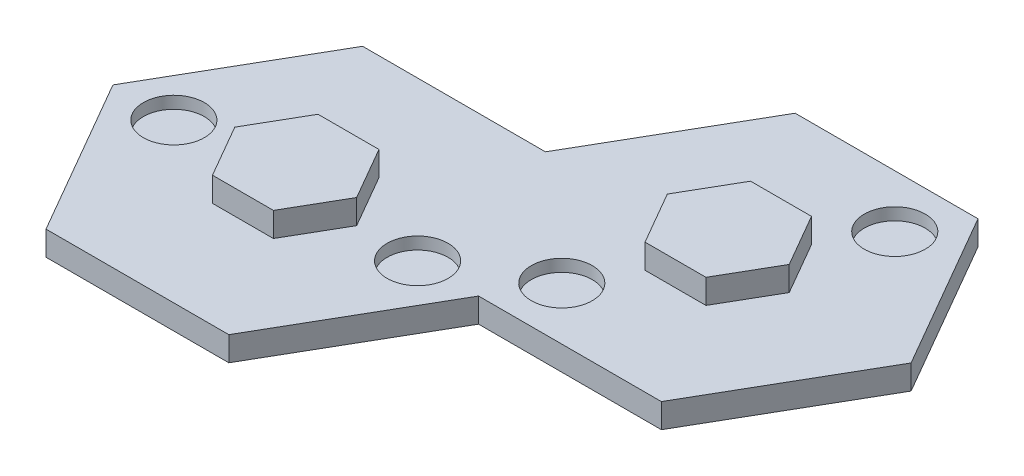
SolidWorks part; units mm, degrees
ref_plane "Front Plane" through (0, 0, 0) normal (0, 0, 1) x (1, 0, 0)
ref_plane "Top Plane" through (0, 0, 0) normal (0, 1, 0) x (1, 0, 0)
ref_plane "Right Plane" through (0, 0, 0) normal (1, 0, 0) x (0, 0, -1)
sketch "Sketch1" plane through (0, 0, 0) normal (0, 1, 0) x (1, 0, 0)
  line L1 (38.1, 65.9911) -> (-38.1, 65.9911)
  line L2 (-38.1, 65.9911) -> (-76.2, 0)
  line L3 (-76.2, 0) -> (-38.1, -65.9911)
  line L4 (-38.1, -65.9911) -> (38.1, -65.9911)
  line L5 (38.1, -65.9911) -> (76.2, 0)
  line L6 (76.2, 0) -> (38.1, 65.9911)
  circle A0 centre (0, 0) radius 65.9911 construction
  dimension "D1" = 76.2
extrude "Boss-Extrude1" add sketch "Sketch1" along normal blind 10.16
sketch "Sketch2" plane through (0, 10.16, 0) normal (0, 1, 0) x (1, 0, 0)
  line L3 (0, -65.9911) -> (0, 65.9911) construction
  line L4 (-38.1, -65.9911) -> (38.1, -65.9911) construction
  line L5 (38.1, 65.9911) -> (-38.1, 65.9911) construction
  circle A0 centre (-50.8, 0) radius 12.7
  circle A1 centre (50.8, 0) radius 12.7
  point P15 (0, 0)
  dimension "D1" = 25.4
  dimension "D2" = 50.8
extrude "Cut-Extrude1" cut sketch "Sketch2" against normal blind 5.08
mirror "Mirror1" about plane through (76.2, 10.16, 0) normal (-0.866, 0, 0.5) of "Boss-Extrude1", "Cut-Extrude1"
sketch "Sketch3" plane through (0, 10.16, 0) normal (0, 1, 0) x (1, 0, 0)
  line L1 (12.7, 21.997) -> (-12.7, 21.997)
  line L2 (-12.7, 21.997) -> (-25.4, 0)
  line L3 (-25.4, 0) -> (-12.7, -21.997)
  line L4 (-12.7, -21.997) -> (12.7, -21.997)
  line L5 (12.7, -21.997) -> (25.4, 0)
  line L6 (25.4, 0) -> (12.7, 21.997)
  circle A0 centre (0, 0) radius 21.997 construction
  dimension "D1" = 25.4
extrude "Boss-Extrude2" add sketch "Sketch3" along normal blind 10.16
ref_plane "Plane1" through (57.15, 0, -32.9956) normal (0.866, 0, -0.5) x (-0.5, 0, -0.866)
mirror "Mirror2" about plane through (57.15, 0, -32.9956) normal (0.866, 0, -0.5) of "Boss-Extrude2"
